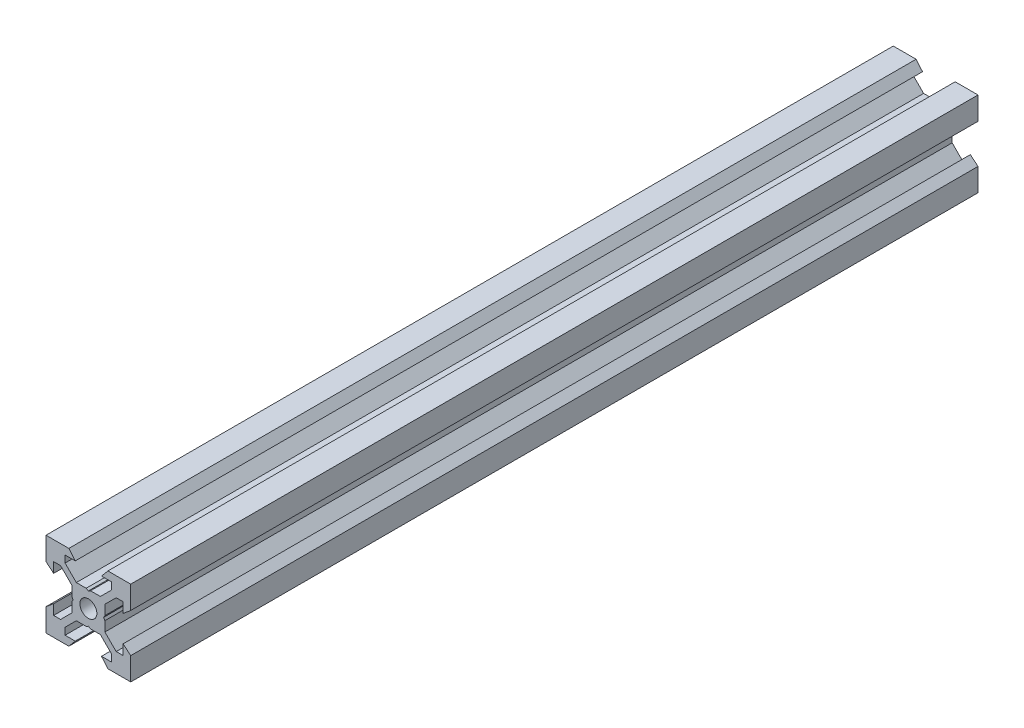
SolidWorks part; units mm, degrees
ref_plane "Front Plane" through (0, 0, 0) normal (0, 0, 1) x (1, 0, 0)
ref_plane "Top Plane" through (0, 0, 0) normal (0, 1, 0) x (1, 0, 0)
ref_plane "Right Plane" through (0, 0, 0) normal (1, 0, 0) x (0, 0, -1)
sketch "Sketch1" plane through (0, 0, 0) normal (0, 0, 1) x (1, 0, 0)
  line L0 (10, 10) -> (4.6104, 10) construction
  line L1 (10, 10) -> (10, 4.6104) construction
  line L2 (10, -10) -> (10, -4.6104) construction
  line L3 (10, -10) -> (4.6104, -10) construction
  line L4 (10, 10) -> (10, 4.6104)
  line L5 (6.5607, 5.5) -> (8.2, 5.5)
  line L6 (5.5, 8.2) -> (5.5, 6.5607)
  line L7 (10, 10) -> (4.6104, 10)
  line L8 (10, 10) -> (10, 4.6104)
  line L9 (6.5607, 5.5) -> (3.9, 2.8393)
  line L10 (5.5, 6.5607) -> (2.8393, 3.9)
  line L11 (10, 4.6104) -> (8.2, 3.1)
  line L12 (4.6104, 10) -> (3.1, 8.2)
  line L13 (8.2, 3.1) -> (8.2, 5.5)
  line L14 (3.1, 8.2) -> (5.5, 8.2)
  line L15 (-6.5607, 5.5) -> (-8.2, 5.5)
  line L16 (6.5607, -5.5) -> (8.2, -5.5)
  line L17 (3.1, -8.2) -> (5.5, -8.2)
  line L18 (8.2, -3.1) -> (8.2, -5.5)
  line L19 (4.6104, -10) -> (3.1, -8.2)
  line L20 (10, -4.6104) -> (8.2, -3.1)
  line L21 (0.5196, -3.9) -> (0, -3.6)
  line L22 (0.5196, 3.9) -> (0, 3.6)
  line L23 (3.6, 0) -> (3.9, -0.5196)
  line L24 (3.9, 0.5196) -> (3.6, 0)
  line L25 (3.9, 0.5196) -> (3.9, 2.8393)
  line L26 (2.8393, 3.9) -> (0.5196, 3.9)
  line L27 (3.9, -2.8393) -> (3.9, -0.5196)
  line L28 (2.8393, -3.9) -> (0.5196, -3.9)
  line L29 (5.5, -6.5607) -> (2.8393, -3.9)
  line L30 (6.5607, -5.5) -> (3.9, -2.8393)
  line L31 (10, -10) -> (10, -4.6104)
  line L32 (10, -10) -> (4.6104, -10)
  line L33 (5.5, -8.2) -> (5.5, -6.5607)
  line L34 (-6.5607, -5.5) -> (-8.2, -5.5)
  line L35 (10, -10) -> (10, -4.6104)
  line L36 (0, 0) -> (0, 8.2) construction
  line L37 (-10, -10) -> (-4.6104, -10) construction
  line L38 (-10, -10) -> (-10, -4.6104) construction
  line L39 (-10, 10) -> (-10, 4.6104) construction
  line L40 (-10, 10) -> (-4.6104, 10) construction
  line L41 (-10, -10) -> (-10, -4.6104)
  line L43 (-5.5, -8.2) -> (-5.5, -6.5607)
  line L44 (-10, -10) -> (-4.6104, -10)
  line L45 (-10, -10) -> (-10, -4.6104)
  line L46 (-6.5607, -5.5) -> (-3.9, -2.8393)
  line L47 (-5.5, -6.5607) -> (-2.8393, -3.9)
  line L48 (-2.8393, -3.9) -> (-0.5196, -3.9)
  line L49 (-3.9, -2.8393) -> (-3.9, -0.5196)
  line L50 (-2.8393, 3.9) -> (-0.5196, 3.9)
  line L51 (-3.9, 0.5196) -> (-3.9, 2.8393)
  line L52 (-3.9, 0.5196) -> (-3.6, 0)
  line L53 (-3.6, 0) -> (-3.9, -0.5196)
  line L54 (-0.5196, 3.9) -> (0, 3.6)
  line L55 (-0.5196, -3.9) -> (0, -3.6)
  line L56 (-10, -4.6104) -> (-8.2, -3.1)
  line L57 (-4.6104, -10) -> (-3.1, -8.2)
  line L58 (-8.2, -3.1) -> (-8.2, -5.5)
  line L59 (-3.1, -8.2) -> (-5.5, -8.2)
  line L60 (-10, -10) -> (10, -10) construction
  line L61 (-10, -10) -> (-10, 10) construction
  line L62 (-3.1, 8.2) -> (-5.5, 8.2)
  line L63 (-8.2, 3.1) -> (-8.2, 5.5)
  line L64 (-4.6104, 10) -> (-3.1, 8.2)
  line L65 (-10, 4.6104) -> (-8.2, 3.1)
  line L66 (-5.5, 6.5607) -> (-2.8393, 3.9)
  line L67 (-6.5607, 5.5) -> (-3.9, 2.8393)
  line L68 (-10, 10) -> (-10, 4.6104)
  line L69 (-10, 10) -> (-4.6104, 10)
  line L70 (-5.5, 8.2) -> (-5.5, 6.5607)
  line L71 (-10, 10) -> (10, 10) construction
  line L72 (-10, 10) -> (-10, 4.6104)
  line L73 (10, -10) -> (10, 10) construction
  line L74 (-10, -10) -> (10, 10) construction
  line L75 (-10, 10) -> (10, -10) construction
  circle A0 centre (0, 0) radius 2
  dimension "D7" = 4
  dimension "D1" = 20
  dimension "D2" = 5.3896
  dimension "D3" = 4.5
  dimension "D4" = 50
  dimension "D5" = 1.8
  dimension "D6" = 1.5104
  dimension "D8" = 5.5
  dimension "D9" = 120
  dimension "D10" = 0.3
  dimension "D11" = 2.3197
  dimension "D12" = 7.8
  dimension "D13" = 7.8
  dimension "D14" = 1.5
  dimension "D15" = 2.6607
extrude "Boss-Extrude1" add sketch "Sketch1" along normal mid plane 200 contours L70 L62 L64 L69 L68 L65 L63 L15 L67 L51 L52 L53 L49 L46 L34 L58 L56 L41 L44 L57 L59 L43 L47 L48 L55 L21 L28 L29 L33 L17 L19 L32 L31 L20 L18 L16 L30 L27 L23 L24 L25 L9 L5 L13 L11 L4 L7 L12 L14 L6 L10
